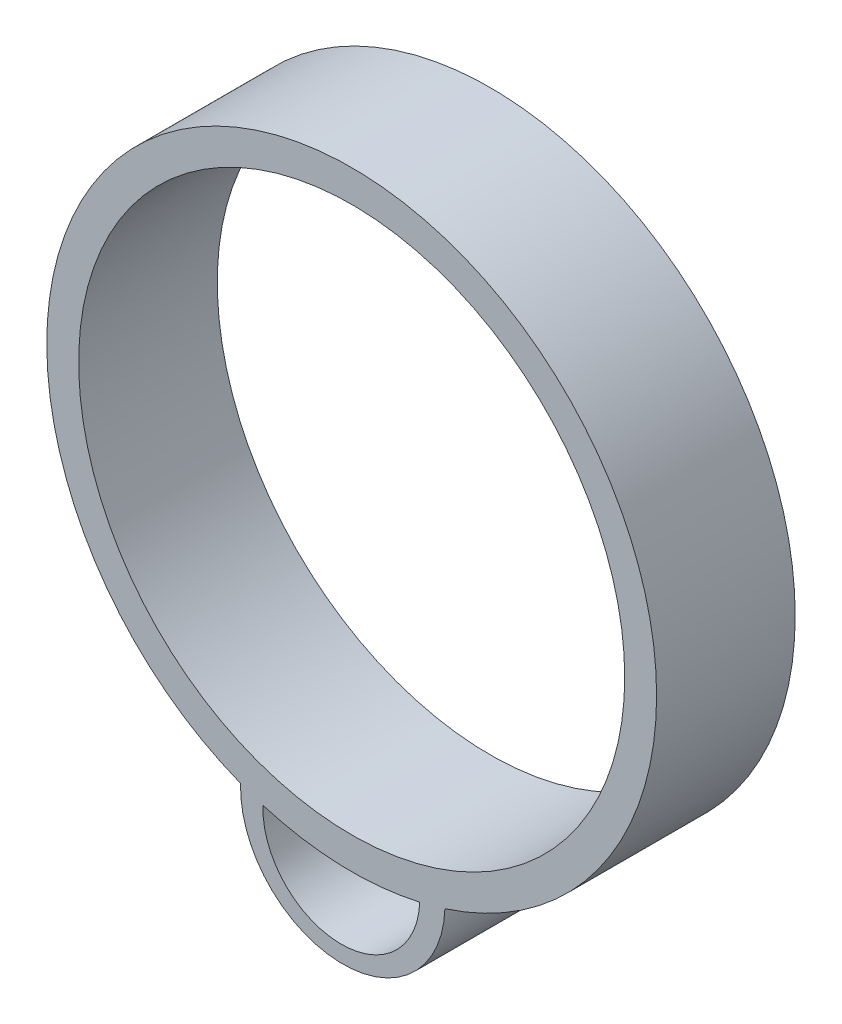
SolidWorks part; units mm, degrees
ref_plane "Front Plane" through (0, 0, 0) normal (0, 0, 1) x (1, 0, 0)
ref_plane "Top Plane" through (0, 0, 0) normal (0, 1, 0) x (1, 0, 0)
ref_plane "Right Plane" through (0, 0, 0) normal (1, 0, 0) x (0, 0, -1)
sketch "Sketch1" plane through (0, 0, 0) normal (0, 0, 1) x (1, 0, 0)
  circle A0 centre (0, 0) radius 25.019
  arc A1 (-10.1828, -26.0183) -> (8.5398, -26.6029) centre (-0.8215, -26.3106) ccw
  arc A2 (-8.1319, -26.7304) -> (6.2316, -27.2362) centre (-0.9501, -26.9833) ccw
  circle A3 centre (0, 0) radius 27.94
  dimension "D1" = 50.038
  dimension "D2" = 55.88
extrude "Boss-Extrude1" add sketch "Sketch1" along normal blind 12.7 contours A3 A1 A2 | A3 A0
